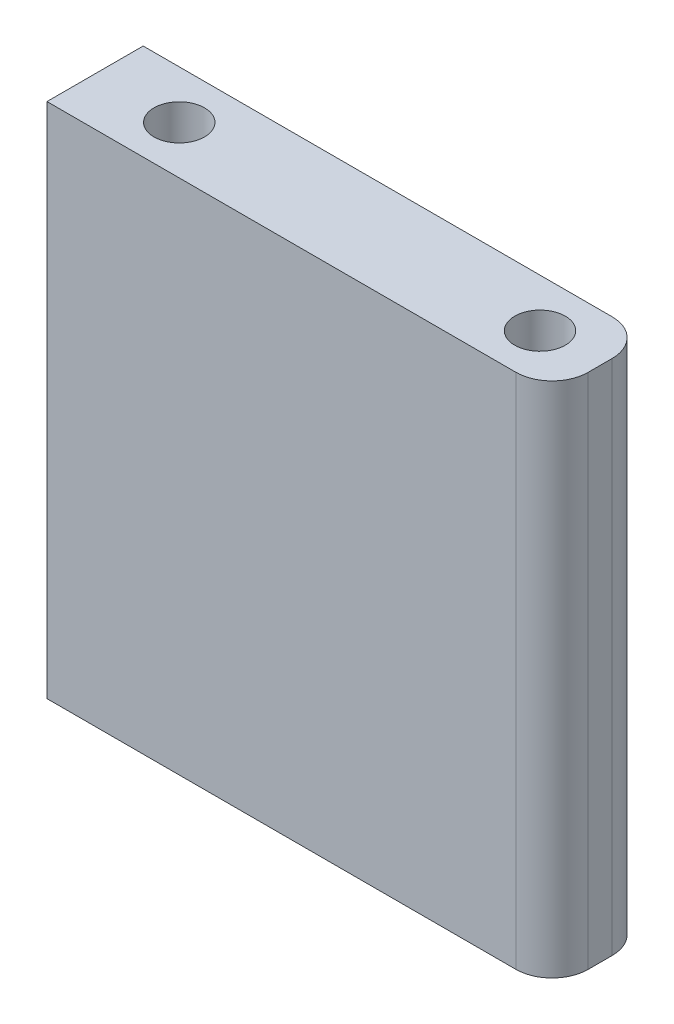
SolidWorks part; units mm, degrees
ref_plane "Front Plane" through (0, 0, 0) normal (0, 0, 1) x (1, 0, 0)
ref_plane "Top Plane" through (0, 0, 0) normal (0, 1, 0) x (1, 0, 0)
ref_plane "Right Plane" through (0, 0, 0) normal (1, 0, 0) x (0, 0, -1)
sketch "Sketch1" plane through (0, 0, 0) normal (0, 0, 1) x (1, 0, 0)
  line L1 (0, 0) -> (42, 0)
  line L2 (0, 0) -> (0, 43)
  line L3 (0, 43) -> (42, 43)
  line L4 (42, 0) -> (42, 43)
  dimension "D1" = 43
  dimension "D2" = 42
extrude "Boss-Extrude1" add sketch "Sketch1" along normal blind 8
sketch "Sketch2" plane through (0, 0, 0) normal (0, -1, 0) x (1, 0, 0)
  line L2 (42, 8) -> (42, 0) construction
  line L3 (42, 4) -> (37, 4)
  circle A0 centre (37, 4) radius 2.1
  circle A1 centre (7, 4) radius 2.1
extrude "Cut-Extrude1" cut sketch "Sketch2" against normal blind 10
sketch "Sketch3" plane through (0, 43, 0) normal (0, 1, 0) x (1, 0, 0)
  circle A0 centre (37, -4) radius 2.1
  circle A1 centre (7, -4) radius 2.1
extrude "Cut-Extrude2" cut sketch "Sketch3" against normal blind 10
fillet "Fillet1" radius 3 2 edges at (42, 21.5, 0) (42, 21.5, 8)
